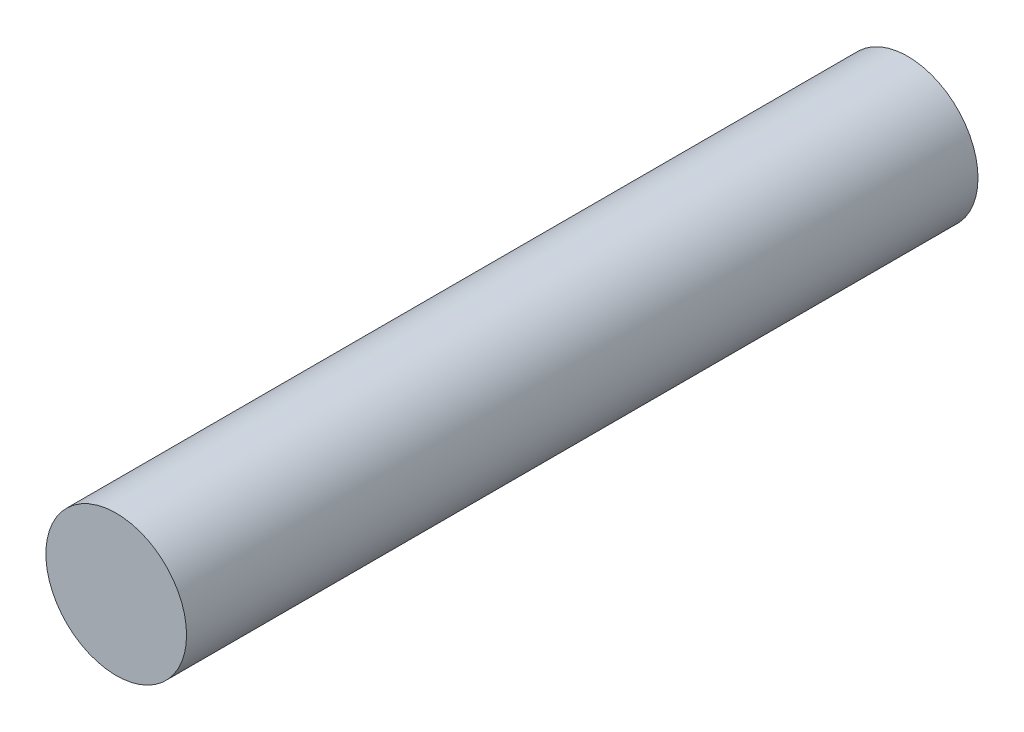
SolidWorks part; units mm, degrees
ref_plane "Front Plane" through (0, 0, 0) normal (0, 0, 1) x (1, 0, 0)
ref_plane "Top Plane" through (0, 0, 0) normal (0, 1, 0) x (1, 0, 0)
ref_plane "Right Plane" through (0, 0, 0) normal (1, 0, 0) x (0, 0, -1)
sketch "Sketch2" plane through (0, 0, 0) normal (0, 0, 1) x (1, 0, 0)
  circle A0 centre (0, 0) radius 2.5
  circle A1 centre (0, 0) radius 4
  dimension "D1" = 5
  dimension "D2" = 8
extrude "Boss-Extrude1" add sketch "Sketch2" along normal blind 5
sketch "Sketch3" plane through (0, 0, 5) normal (0, 0, 1) x (1, 0, 0)
  circle A0 centre (0, 0) radius 4
  dimension "D1" = 8
extrude "Boss-Extrude2" add sketch "Sketch3" along normal blind 40
